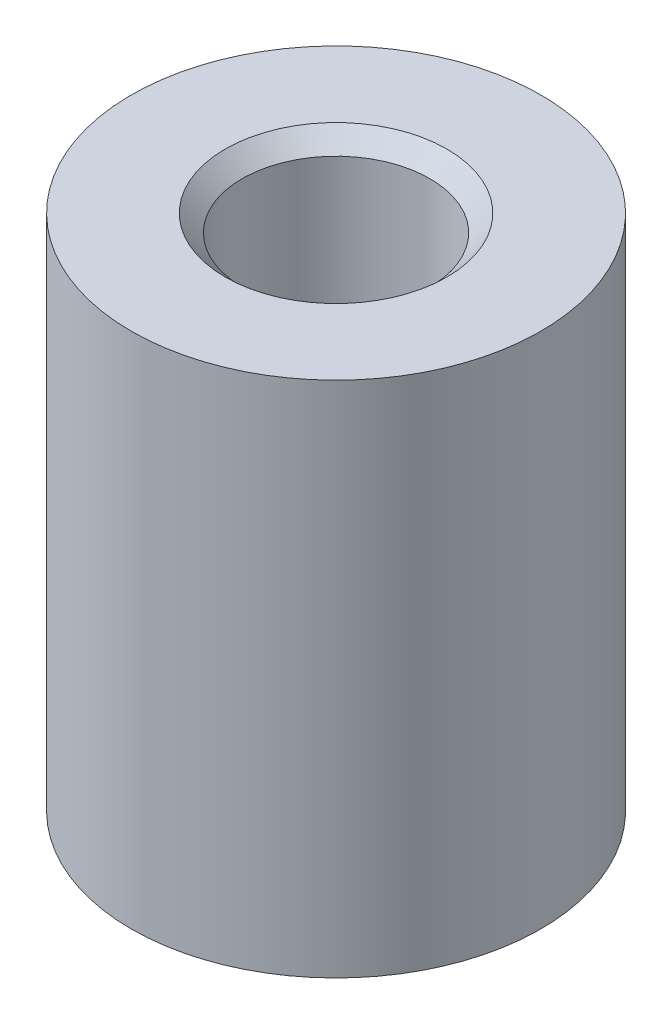
SolidWorks part; units mm, degrees
ref_plane "Front Plane" through (0, 0, 0) normal (0, 0, 1) x (1, 0, 0)
ref_plane "Top Plane" through (0, 0, 0) normal (0, 1, 0) x (1, 0, 0)
ref_plane "Right Plane" through (0, 0, 0) normal (1, 0, 0) x (0, 0, -1)
sketch "Sketch1" plane through (0, 0, 0) normal (0, 1, 0) x (1, 0, 0)
  circle A0 centre (0, 0) radius 2
  circle A1 centre (0, 0) radius 6
  dimension "D1" = 4
  dimension "D2" = 12
extrude "Boss-Extrude1" add sketch "Sketch1" along normal blind 7.5875 and the other way blind 7.5875
sketch "Sketch2" plane through (0, 7.5875, 0) normal (0, 1, 0) x (1, 0, 0)
  circle A0 centre (0, 0) radius 2.75
  dimension "D1" = 5.5
extrude "Cut-Extrude1" cut sketch "Sketch2" against normal through all
sketch "Sketch5" plane through (0, 7.5875, 0) normal (0, 1, 0) x (1, 0, 0)
  circle A0 centre (0, 0) radius 3.25
  circle A1 centre (0, 0) radius 2.75 construction
  dimension "D1" = 0.5
extrude "Cut-Extrude3" cut sketch "Sketch5" against normal blind 8 draft 45
mirror "Mirror1" about plane through (0, 0, 0) normal (0, 1, 0) of "Cut-Extrude3"
